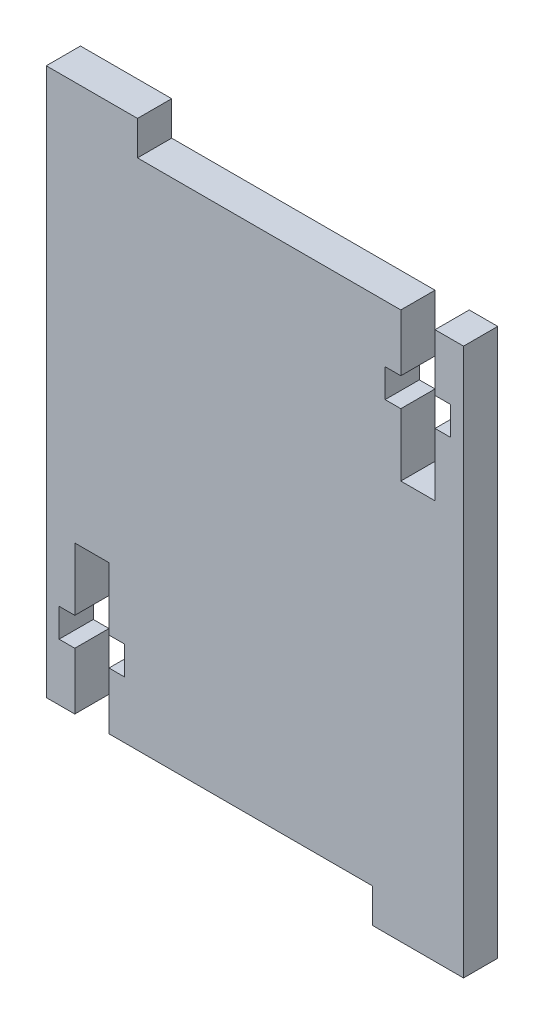
SolidWorks part; units mm, degrees
ref_plane "Plano frontal" through (0, 0, 0) normal (0, 0, 1) x (1, 0, 0)
ref_plane "Plano superior" through (0, 0, 0) normal (0, 1, 0) x (1, 0, 0)
ref_plane "Plano direito" through (0, 0, 0) normal (1, 0, 0) x (0, 0, -1)
sketch "Esboço1" plane through (0, 0, 0) normal (0, 0, 1) x (1, 0, 0)
  line L0 (-23.1902, 33.6525) -> (-23.1902, 30.6525)
  line L2 (-31.1902, 30.6525) -> (-31.1902, 33.6525)
  line L3 (-31.1902, 33.6525) -> (-23.1902, 33.6525)
  line L4 (-31.1902, 30.6525) -> (-31.1902, -14.3475)
  line L5 (-30.0652, -6.8475) -> (-30.0652, -9.3475)
  line L6 (-25.6902, -14.3475) -> (-25.6902, -9.3475)
  line L7 (-25.6902, -1.3475) -> (-28.6902, -1.3475)
  line L8 (-28.6902, -1.3475) -> (-28.6902, -6.8475)
  line L9 (-24.3152, -6.8475) -> (-25.6902, -6.8475)
  line L10 (-30.0652, -9.3475) -> (-28.6902, -9.3475)
  line L11 (-24.3152, -9.3475) -> (-24.3152, -6.8475)
  line L12 (-25.6902, -9.3475) -> (-24.3152, -9.3475)
  line L13 (-25.6902, -6.8475) -> (-25.6902, -1.3475)
  line L14 (-28.6902, -6.8475) -> (-30.0652, -6.8475)
  line L15 (-28.6902, -9.3475) -> (-28.6902, -14.3475)
  line L16 (-31.1902, -14.3475) -> (-28.6902, -14.3475)
  line L17 (4.2848, 23.1525) -> (4.2848, 25.6525)
  line L18 (-0.0902, 30.6525) -> (-0.0902, 25.6525)
  line L19 (-0.0902, 17.6525) -> (2.9098, 17.6525)
  line L20 (2.9098, 17.6525) -> (2.9098, 23.1525)
  line L21 (-1.4652, 23.1525) -> (-0.0902, 23.1525)
  line L22 (4.2848, 25.6525) -> (2.9098, 25.6525)
  line L23 (-1.4652, 25.6525) -> (-1.4652, 23.1525)
  line L24 (-0.0902, 25.6525) -> (-1.4652, 25.6525)
  line L25 (-0.0902, 23.1525) -> (-0.0902, 17.6525)
  line L26 (2.9098, 23.1525) -> (4.2848, 23.1525)
  line L27 (2.9098, 25.6525) -> (2.9098, 30.6525)
  line L28 (2.9098, 30.6525) -> (5.4098, 30.6525)
  line L29 (5.4098, 30.6525) -> (5.4098, -14.3475)
  line L30 (-2.5902, -14.3475) -> (-25.6902, -14.3475)
  line L31 (-0.0902, 30.6525) -> (-23.1902, 30.6525)
  line L32 (5.4098, -14.3475) -> (5.4098, -17.3475)
  line L33 (5.4098, -17.3475) -> (-2.5902, -17.3475)
  line L34 (-2.5902, -17.3475) -> (-2.5902, -14.3475)
extrude "Ressalto-extrusão1" add sketch "Esboço1" along normal blind 3
